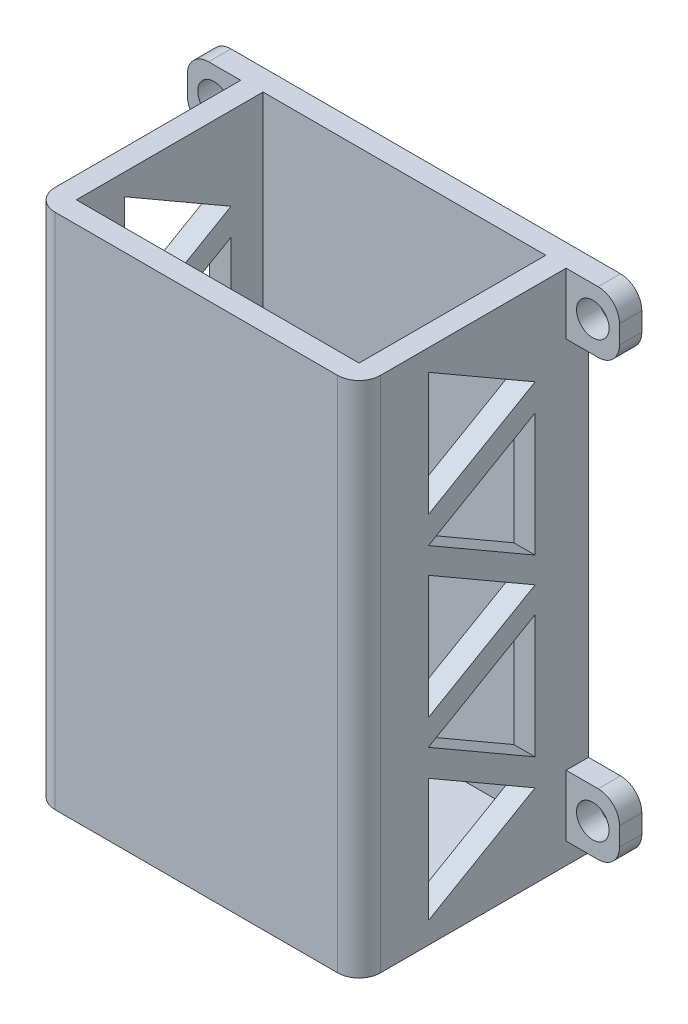
SolidWorks part; units mm, degrees
ref_plane "Front Plane" through (0, 0, 0) normal (0, 0, 1) x (1, 0, 0)
ref_plane "Top Plane" through (0, 0, 0) normal (0, 1, 0) x (1, 0, 0)
ref_plane "Right Plane" through (0, 0, 0) normal (1, 0, 0) x (0, 0, -1)
sketch "Sketch1" plane through (0, 0, 0) normal (0, 1, 0) x (1, 0, 0)
  line L0 (15.25, -10.75) -> (15.25, 10.75)
  line L1 (-13.25, -8.75) -> (13.25, -8.75)
  line L2 (-13.25, -8.75) -> (-13.25, 8.75)
  line L3 (-13.25, 8.75) -> (13.25, 8.75)
  line L4 (13.25, -8.75) -> (13.25, 8.75)
  line L5 (-13.25, -8.75) -> (13.25, 8.75) construction
  line L6 (-13.25, 8.75) -> (13.25, -8.75) construction
  line L7 (-15.25, 10.75) -> (15.25, 10.75)
  line L8 (-15.25, -10.75) -> (-15.25, 10.75)
  line L9 (-15.25, -10.75) -> (15.25, -10.75)
  point P0 (0, 0)
  dimension "D1" = 26.5
  dimension "D2" = 17.5
  dimension "D3" = 2
extrude "Boss-Extrude1" add sketch "Sketch1" along normal blind 46.5
fillet "Fillet1" radius 2 2 edges at (-15.25, 23.25, 10.75) (15.25, 23.25, 10.75)
sketch "Sketch2" plane through (-15.25, 0, 0) normal (-1, 0, 0) x (0, 0, 1)
  line L1 (-10.75, 0) -> (-8.6559, 0)
  line L2 (-10.75, 0) -> (-10.75, 5.7485)
  line L3 (-10.75, 5.7485) -> (-8.6559, 5.7485)
  line L4 (-8.6559, 0) -> (-8.6559, 5.7485)
extrude "Boss-Extrude2" add sketch "Sketch2" along normal blind 5
sketch "Sketch3" plane through (0, 0, -8.6559) normal (0, 0, 1) x (1, 0, 0)
  line L0 (-20.25, 0) -> (-15.25, 0) construction
  line L1 (-17.75, 2.8743) -> (-17.75, 0) construction
  line L2 (-17.75, 0) -> (-17.75, 2.8743) construction
  line L3 (-17.75, 2.8743) -> (-20.25, 2.8743) construction
  line L4 (-20.25, 0) -> (-20.25, 5.7485) construction
  circle A0 centre (-17.75, 2.8743) radius 1.525
  dimension "D1" = 3.05
extrude "Cut-Extrude1" cut sketch "Sketch3" against normal through all both and the other way through all
ref_plane "Plane1" through (0, 23.25, 0) normal (0, 1, 0) x (1, 0, 0)
mirror "Mirror3" about plane through (0, 23.25, 0) normal (0, 1, 0) of "Cut-Extrude1", "Boss-Extrude2"
mirror "Mirror4" about plane through (0, 0, 0) normal (1, 0, 0) of "Mirror3", "Boss-Extrude2", "Cut-Extrude1"
fillet "Fillet2" radius 2 8 edges at (20.25, 46.5, -9.7029) (20.25, 40.7515, -9.7029) (20.25, 0, -9.7029) (20.25, 5.7485, -9.7029) (-20.25, 5.7485, -9.7029) (-20.25, 0, -9.7029) (-20.25, 40.7515, -9.7029) (-20.25, 46.5, -9.7029)
sketch "Sketch4" plane through (0, 0, 0) normal (0, -1, 0) x (1, 0, 0)
  line L1 (15.25, -10.75) -> (-15.25, -10.75)
  line L2 (15.25, -10.75) -> (15.25, 8.75)
  line L3 (13.25, 10.75) -> (-13.25, 10.75)
  line L4 (-15.25, -10.75) -> (-15.25, 8.75)
  line L5 (-13.25, 10.75) -> (13.25, 10.75) construction
  line L6 (-15.25, -8.6559) -> (-15.25, 8.75) construction
  line L9 (15.25, 8.75) -> (15.25, -8.6559) construction
  line L10 (18.25, -10.75) -> (-18.25, -10.75) construction
  arc A0 (-13.25, 10.75) -> (-15.25, 8.75) centre (-13.25, 8.75) ccw
  arc A1 (13.25, 10.75) -> (15.25, 8.75) centre (13.25, 8.75) cw
  dimension "D1" = 2
  dimension "D2" = 2
extrude "Boss-Extrude4" add sketch "Sketch4" along normal blind 2
sketch "Sketch6" plane through (-15.25, 0, 0) normal (-1, 0, 0) x (0, 0, 1)
  line L0 (-5.75, 46.5) -> (-5.75, -2) construction
  line L1 (-8.6559, 46.5) -> (8.75, 46.5) construction
  line L2 (8.75, -2) -> (-10.75, -2) construction
  line L3 (-10.75, 40.7515) -> (-10.75, 5.7485) construction
  line L4 (4.25, 46.5) -> (4.25, -2) construction
  line L5 (-5.75, 22.25) -> (4.25, 16.4765)
  line L6 (-5.75, 38.7265) -> (4.25, 32.953)
  line L7 (4.25, 32.953) -> (4.25, 44.5)
  line L8 (4.25, 44.5) -> (-5.75, 38.7265)
  line L9 (4.25, 16.4765) -> (4.25, 28.0235)
  line L10 (4.25, 28.0235) -> (-5.75, 22.25)
  line L11 (-5.75, 5.7735) -> (4.25, 0)
  line L12 (4.25, 0) -> (4.25, 11.547)
  line L13 (4.25, 11.547) -> (-5.75, 5.7735)
  line L14 (-5.75, 22.25) -> (4.25, 22.25) construction
  line L15 (4.25, 30.4392) -> (-5.75, 36.2127)
  line L16 (-5.75, 36.2127) -> (-5.75, 24.6657)
  line L17 (-5.75, 24.6657) -> (4.25, 30.4392)
  line L18 (-5.75, 19.8343) -> (4.25, 14.0608)
  line L19 (-5.75, 8.2873) -> (-5.75, 19.8343)
  line L20 (4.25, 14.0608) -> (-5.75, 8.2873)
  circle A0 centre (0.9167, 38.7265) radius 3.3333 construction
  circle A1 centre (-2.4167, 30.4392) radius 3.3333 construction
  dimension "D1" = 5
  dimension "D2" = 10
  dimension "D3" = 2
  dimension "D5" = 2
  dimension "D6" = 2.5138
  dimension "D4" = 3
extrude "Cut-Extrude2" cut sketch "Sketch6" against normal through all both and the other way through all
